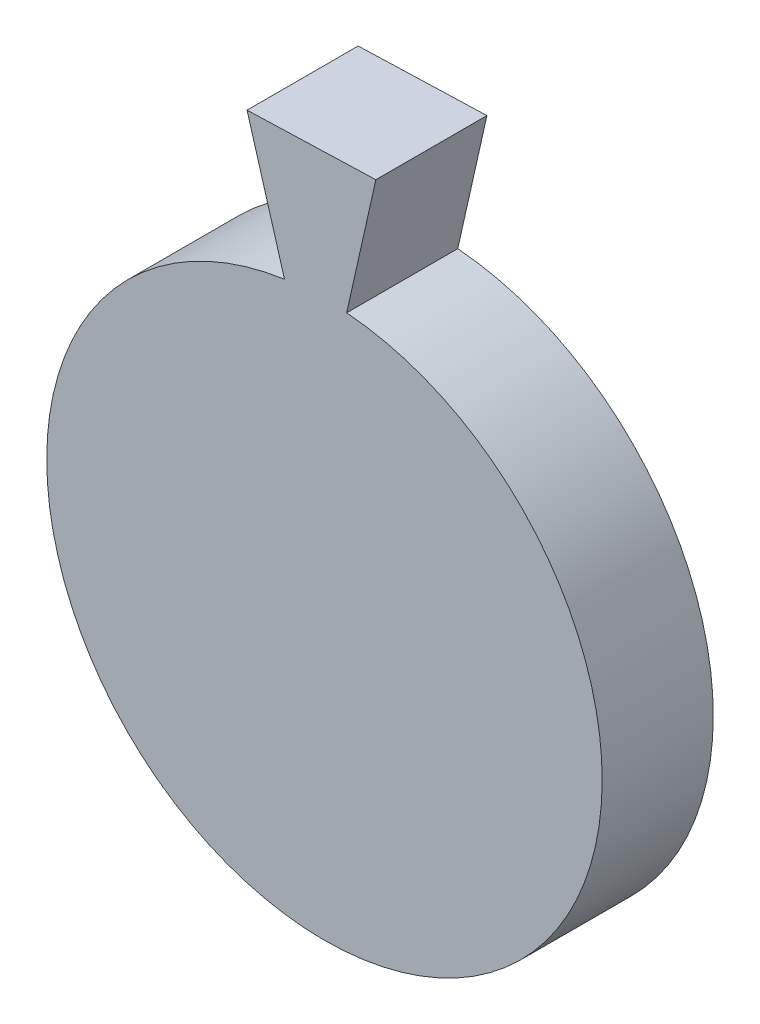
SolidWorks part; units mm, degrees
ref_plane "正面" through (0, 0, 0) normal (0, 0, 1) x (1, 0, 0)
ref_plane "平面" through (0, 0, 0) normal (0, 1, 0) x (1, 0, 0)
ref_plane "右側面" through (0, 0, 0) normal (1, 0, 0) x (0, 0, -1)
sketch "ｽｹｯﾁ1" plane through (0, 0, 0) normal (0, 0, 1) x (1, 0, 0)
  circle A0 centre (-14.8801, 17.6071) radius 12.5
extrude "ﾎﾞｽ - 押し出し1" add sketch "ｽｹｯﾁ1" along normal blind 5
sketch "ｽｹｯﾁ2" plane through (0, 0, 0) normal (0, 0, -1) x (-1, 0, 0)
  line L0 (13.8801, 30.0671) -> (16.6787, 29.9771)
  line L3 (14.0666, 35.8641) -> (16.8651, 35.7741)
  line L4 (16.6787, 29.9771) -> (18.3643, 35.7259)
  line L5 (18.3643, 35.7259) -> (16.8651, 35.7741)
  line L6 (13.8801, 30.0671) -> (12.5673, 35.9123)
  line L7 (12.5673, 35.9123) -> (14.0666, 35.8641)
  circle A0 centre (14.8801, 17.6071) radius 12.5 construction
  dimension "D1" = 2.8
  dimension "D2" = 5.8
  dimension "D3" = 1.5
  dimension "D4" = 1.5
extrude "ﾎﾞｽ - 押し出し2" add sketch "ｽｹｯﾁ2" against normal blind 5
